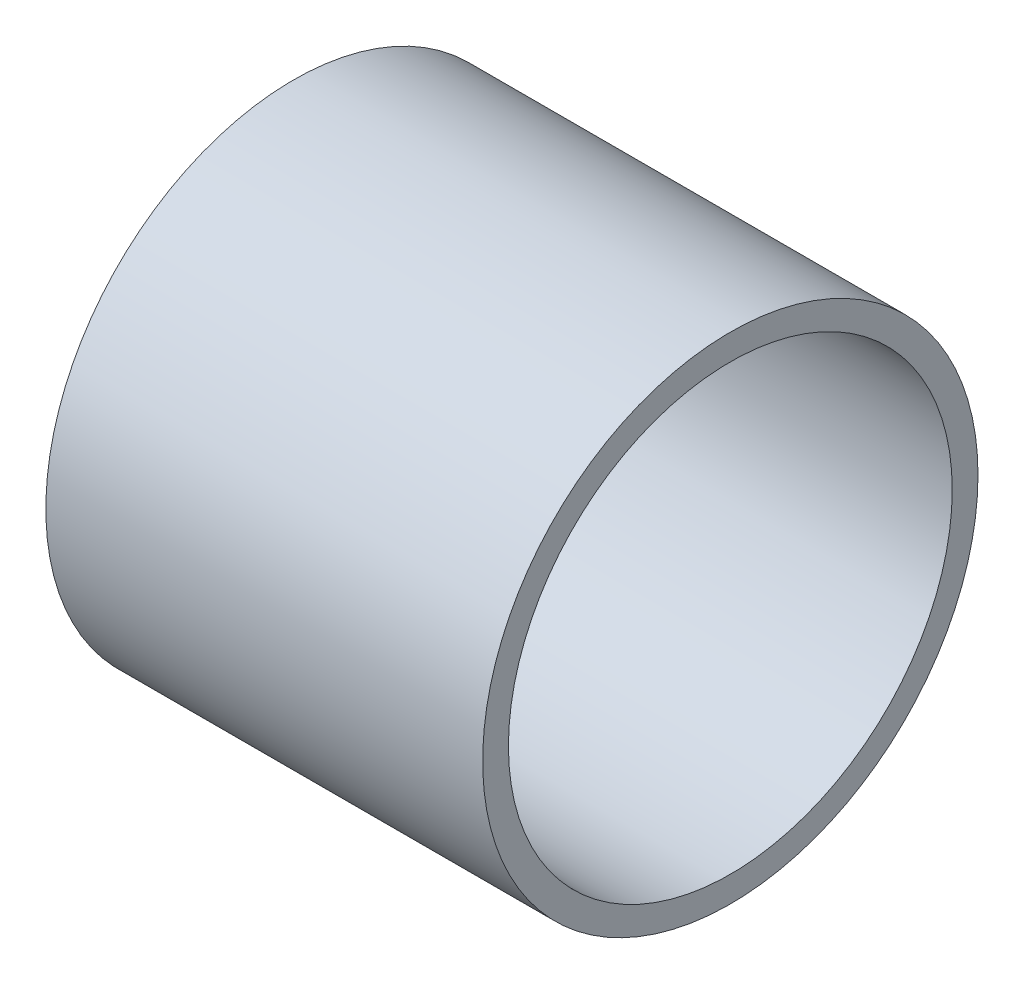
SolidWorks part; units mm, degrees
ref_plane "Front Plane" through (0, 0, 0) normal (0, 0, 1) x (1, 0, 0)
ref_plane "Top Plane" through (0, 0, 0) normal (0, 1, 0) x (1, 0, 0)
ref_plane "Right Plane" through (0, 0, 0) normal (1, 0, 0) x (0, 0, -1)
sketch "Sketch1" plane through (0, 0, 0) normal (1, 0, 0) x (0, 0, -1)
  circle A0 centre (0, 0) radius 15.875
  circle A1 centre (0, 0) radius 14.224
  dimension "D1" = 31.75
  dimension "D2" = 1.651
extrude "Boss-Extrude1" add sketch "Sketch1" along normal blind 28
